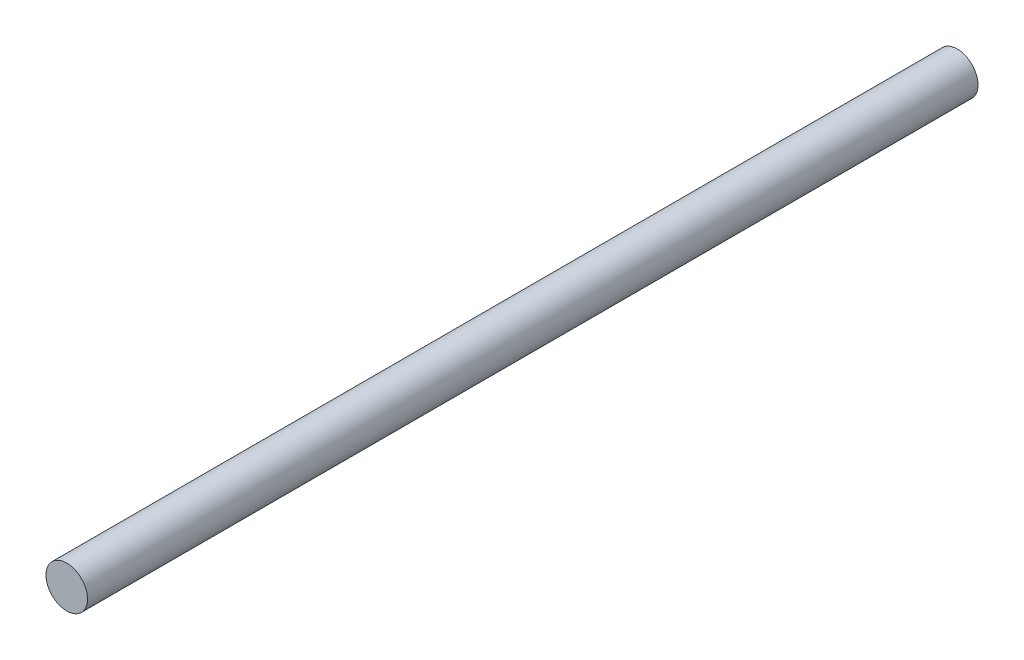
SolidWorks part; units mm, degrees
ref_plane "Front Plane" through (0, 0, 0) normal (0, 0, 1) x (1, 0, 0)
ref_plane "Top Plane" through (0, 0, 0) normal (0, 1, 0) x (1, 0, 0)
ref_plane "Right Plane" through (0, 0, 0) normal (1, 0, 0) x (0, 0, -1)
sketch "Sketch1" plane through (0, 0, 0) normal (0, 0, 1) x (1, 0, 0)
  circle A0 centre (0, 0) radius 0.889
  dimension "D1" = 1.778
extrude "Boss-Extrude1" add sketch "Sketch1" along normal blind 38.1
